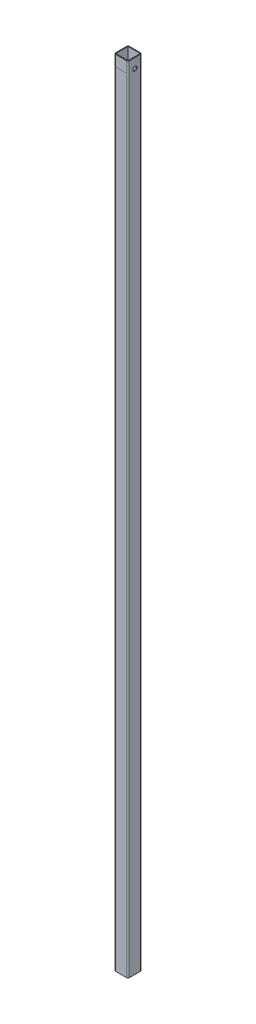
SolidWorks part; units mm, degrees
material "Thornel Mat VMA"
ref_plane "Front Plane" through (0, 0, 0) normal (0, 0, 1) x (1, 0, 0)
ref_plane "Top Plane" through (0, 0, 0) normal (0, 1, 0) x (1, 0, 0)
ref_plane "Right Plane" through (0, 0, 0) normal (1, 0, 0) x (0, 0, -1)
sketch "Sketch1" plane through (0, 0, 0) normal (0, 1, 0) x (1, 0, 0)
  line L1 (-11.4046, -11.4046) -> (11.4046, -11.4046)
  line L2 (-11.4046, -11.4046) -> (-11.4046, 11.4046)
  line L3 (-11.4046, 11.4046) -> (11.4046, 11.4046)
  line L4 (11.4046, -11.4046) -> (11.4046, 11.4046)
  line L5 (-11.4046, -11.4046) -> (11.4046, 11.4046) construction
  line L6 (-11.4046, 11.4046) -> (11.4046, -11.4046) construction
  line L7 (-10.0711, -10.0711) -> (10.0711, -10.0711)
  line L8 (-10.0711, -10.0711) -> (-10.0711, 10.0711)
  line L9 (-10.0711, 10.0711) -> (10.0711, 10.0711)
  line L10 (10.0711, -10.0711) -> (10.0711, 10.0711)
  line L11 (-10.0711, -10.0711) -> (10.0711, 10.0711) construction
  line L12 (-10.0711, 10.0711) -> (10.0711, -10.0711) construction
  point P0 (0, 0)
  point P6 (0, 0)
  dimension "D2" = 22.8092
  dimension "D3" = 20.1422
extrude "Boss-Extrude1" add sketch "Sketch1" along normal blind 1303.02
fillet "Fillet1" radius 2.54 4 edges at (-11.4046, 651.51, 11.4046) (11.4046, 651.51, 11.4046) (11.4046, 651.51, -11.4046) (-11.4046, 651.51, -11.4046)
sketch "Sketch2" plane through (0, 0, 11.4046) normal (0, 0, 1) x (1, 0, 0)
  line L0 (-8.8646, 1303.02) -> (-8.8646, 0) construction
  line L1 (-8.8646, 1285.2908) -> (8.8646, 1285.2908)
  line L2 (-8.8646, 1285.2908) -> (-8.8646, 1303.02)
  line L3 (-8.8646, 1303.02) -> (8.8646, 1303.02)
  line L4 (8.8646, 1285.2908) -> (8.8646, 1303.02)
  line L5 (-8.8646, 1285.2908) -> (8.8646, 1303.02) construction
  line L6 (-8.8646, 1303.02) -> (8.8646, 1285.2908) construction
  line L7 (8.8646, 0) -> (8.8646, 1303.02) construction
  line L9 (-8.8646, 1303.02) -> (8.8646, 1303.02) construction
  point P0 (0, 1294.1554)
split line "Split Line1"
sketch "Sketch3" plane through (0, 0, 0) normal (0, -1, 0) x (1, 0, 0)
  line L4 (8.8646, 11.4046) -> (-8.8646, 11.4046)
  line L5 (-11.4046, 8.8646) -> (-11.4046, -8.8646)
  line L6 (-8.8646, -11.4046) -> (8.8646, -11.4046)
  line L7 (11.4046, -8.8646) -> (11.4046, 8.8646)
  line L9 (-11.4046, 8.8646) -> (-11.4046, -8.8646)
  line L10 (-8.8646, -11.4046) -> (8.8646, -11.4046)
  line L11 (11.4046, -8.8646) -> (11.4046, 8.8646)
  line L12 (8.8646, 11.4046) -> (-8.8646, 11.4046)
  arc A4 (-8.8646, 11.4046) -> (-11.4046, 8.8646) centre (-8.8646, 8.8646) ccw
  arc A5 (-11.4046, -8.8646) -> (-8.8646, -11.4046) centre (-8.8646, -8.8646) ccw
  arc A6 (8.8646, -11.4046) -> (11.4046, -8.8646) centre (8.8646, -8.8646) ccw
  arc A7 (11.4046, 8.8646) -> (8.8646, 11.4046) centre (8.8646, 8.8646) ccw
  arc A8 (-8.8646, 11.4046) -> (-11.4046, 8.8646) centre (-8.8646, 8.8646) ccw
  arc A9 (-11.4046, -8.8646) -> (-8.8646, -11.4046) centre (-8.8646, -8.8646) ccw
  arc A10 (8.8646, -11.4046) -> (11.4046, -8.8646) centre (8.8646, -8.8646) ccw
  arc A11 (11.4046, 8.8646) -> (8.8646, 11.4046) centre (8.8646, 8.8646) ccw
  dimension "D1" = 0
extrude "Boss-Extrude2" [suppressed] add sketch "Sketch3" against normal blind 2.54
hole_wizard "1/4 (0.25) Diameter Hole1" positions "Sketch4" profile "Sketch5" hole size "1/4" standard "ANSI Inch" end condition through all
sketch "Sketch4" plane through (0, 0, 0) normal (0, -1, 0) x (-1, 0, 0)
  point P0 (0, 0)
sketch "Sketch5" plane through (0, 0, 0) normal (1, 0, 0) x (0, 0, -1)
  line L0 (0, 0) -> (0, 1303.02)
  line L1 (0, 1303.02) -> (3.175, 1303.02)
  line L2 (3.175, 1303.02) -> (3.175, 0)
  line L5 (3.175, 0) -> (0, 0)
  line L11 (0, -6.35) -> (0, 107.95) construction
  dimension "Thru Hole Dia." = 6.35
  dimension "Thru Hole Depth" = 1303.02
hole_wizard "1/4 Clearance Hole1" positions "Sketch6" profile "Sketch7" hole size "1/4" standard "ANSI Inch" end condition through all
sketch "Sketch6" plane through (11.4046, 0, 0) normal (1, 0, 0) x (0, 0, -1)
  line L0 (-8.8646, 1303.02) -> (8.8646, 1303.02) construction
  point P0 (0, 1287.145)
  dimension "D1" = 15.875
sketch "Sketch7" plane through (11.4046, 1287.145, 0) normal (0, 1, 0) x (0, 0, -1)
  line L0 (0, 0) -> (0, 22.8092)
  line L1 (0, 22.8092) -> (3.3782, 22.8092)
  line L2 (3.3782, 22.8092) -> (3.3782, 0)
  line L5 (3.3782, 0) -> (0, 0)
  line L11 (0, -6.35) -> (0, 107.95) construction
  dimension "Thru Hole Dia." = 6.7564
  dimension "Thru Hole Depth" = 22.8092
sketch "Sketch8" plane through (0, 0, -11.4046) normal (0, 0, -1) x (-1, 0, 0)
  line L0 (-8.8646, 1303.02) -> (-8.8646, 0) construction
  line L1 (-8.8646, 241.3) -> (8.8646, 241.3)
  line L2 (-8.8646, 241.3) -> (-8.8646, 259.0292)
  line L3 (-8.8646, 259.0292) -> (8.8646, 259.0292)
  line L4 (8.8646, 241.3) -> (8.8646, 259.0292)
  line L5 (8.8646, 0) -> (8.8646, 1303.02) construction
  dimension "D1" = 241.3
split line "Split Line2"
